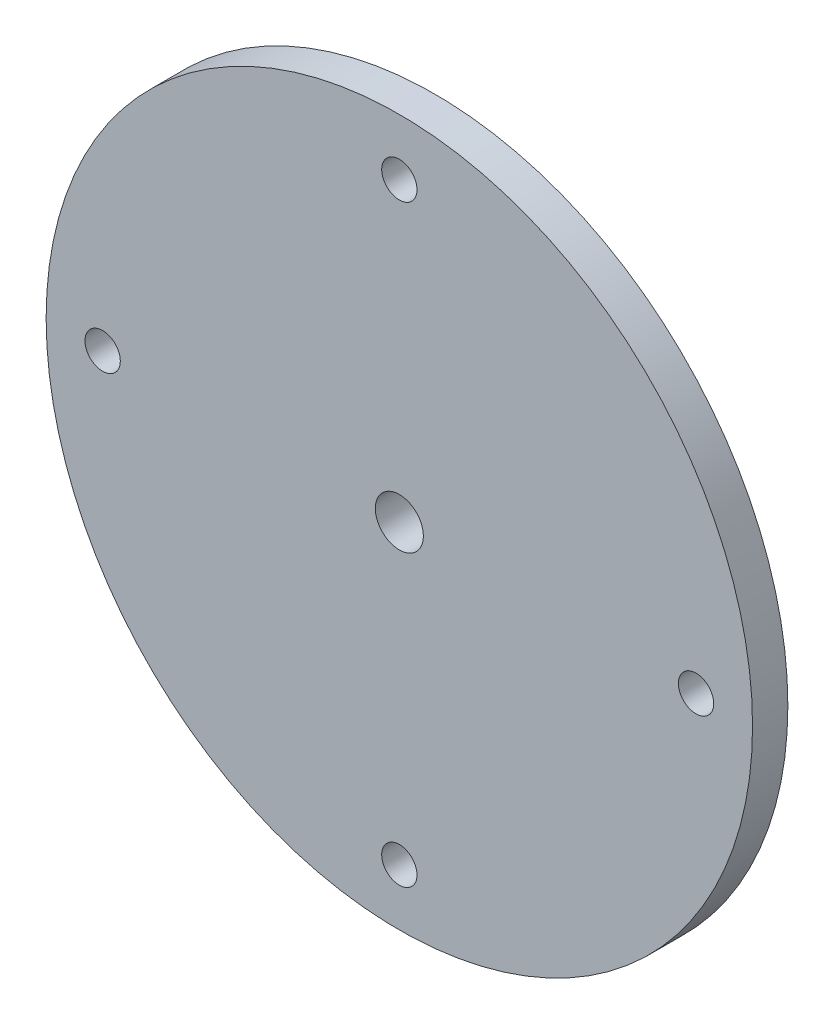
SolidWorks part; units mm, degrees
material "6061 Alloy"
ref_plane "Front Plane" through (0, 0, 0) normal (0, 0, 1) x (1, 0, 0)
ref_plane "Top Plane" through (0, 0, 0) normal (0, 1, 0) x (1, 0, 0)
ref_plane "Right Plane" through (0, 0, 0) normal (1, 0, 0) x (0, 0, -1)
sketch "Sketch1" plane through (0, 0, 0) normal (0, 0, 1) x (1, 0, 0)
  circle A0 centre (0, 0) radius 14
  circle A1 centre (0, 0) radius 12.5
  dimension "D1" = 28
  dimension "D2" = 25
extrude "Boss-Extrude1" add sketch "Sketch1" along normal blind 2
sketch "Sketch2" plane through (0, 0, 2) normal (0, 0, 1) x (1, 0, 0)
  line L1 (-8.8388, -8.8388) -> (8.8388, -8.8388)
  line L2 (-8.8388, -8.8388) -> (-8.8388, 8.8388)
  line L3 (-8.8388, 8.8388) -> (8.8388, 8.8388)
  line L4 (8.8388, -8.8388) -> (8.8388, 8.8388)
  line L5 (-8.8388, -8.8388) -> (8.8388, 8.8388) construction
  line L6 (-8.8388, 8.8388) -> (8.8388, -8.8388) construction
  circle A0 centre (0, 0) radius 12.5 construction
  circle A1 centre (0, 0) radius 14
  point P0 (0, 0)
  dimension "D1" = 28
extrude "Boss-Extrude2" add sketch "Sketch2" along normal blind 5
sketch "Sketch3" plane through (0, 0, 7) normal (0, 0, 1) x (1, 0, 0)
  circle A0 centre (0, 0) radius 14
  dimension "D1" = 28
extrude "Boss-Extrude3" add sketch "Sketch3" along normal blind 5
sketch "Sketch6" plane through (0, 0, 12) normal (0, 0, 1) x (1, 0, 0)
  circle A0 centre (0, 0) radius 50
  dimension "D1" = 100
extrude "Boss-Extrude4" add sketch "Sketch6" against normal blind 5
hole_wizard "M8x1.25 Tapped Hole1" positions "Sketch7" profile "Sketch8" tap size "M8x1.25" standard "ANSI Metric" end condition through all
sketch "Sketch7" plane through (0, 0, 12) normal (0, 0, 1) x (1, 0, 0)
  point P0 (0, 0)
cosmetic thread "Hole Thread1" parameters "D2"=8
sketch "Sketch8" plane through (0, 0, 12) normal (1, 0, 0) x (0, -1, 0)
  line L0 (0, 0) -> (0, 12)
  line L1 (0, 12) -> (3.4, 12)
  line L2 (3.4, 12) -> (3.4, 0)
  line L5 (3.4, 0) -> (0, 0)
  line L11 (0, -6.35) -> (0, 107.95) construction
  dimension "Thru Tap Drill Dia." = 6.8
  dimension "Thru Tap Drill Depth" = 12
hole_wizard "M6x1.0 Tapped Hole1" positions "Sketch9" profile "Sketch10" tap size "M6x1.0" standard "ANSI Metric" end condition through all
sketch "Sketch9" plane through (0, 0, 12) normal (0, 0, 1) x (1, 0, 0)
  line L0 (0, -6.6) -> (0, 6.6) construction
  line L1 (6.6, 0) -> (-6.6, 0) construction
  circle A0 centre (0, 0) radius 42
  point P0 (0, 42)
  point P4 (42, 0)
  point P8 (0, -42)
  point P10 (-42, 0)
  dimension "D1" = 84
sketch "Sketch10" plane through (0, 42, 12) normal (1, 0, 0) x (0, -1, 0)
  line L0 (0, 0) -> (0, 12)
  line L1 (0, 12) -> (2.5, 12)
  line L2 (2.5, 12) -> (2.5, 0)
  line L5 (2.5, 0) -> (0, 0)
  line L11 (0, -6.35) -> (0, 107.95) construction
  dimension "Thru Tap Drill Dia." = 5
  dimension "Thru Tap Drill Depth" = 12
cosmetic thread "Hole Thread2" parameters "D2"=6
cosmetic thread "Hole Thread3" parameters "D2"=6
cosmetic thread "Hole Thread4" parameters "D2"=6
cosmetic thread "Hole Thread5" parameters "D2"=6
fillet "Fillet1" radius 6 1 edges at (14, 0, 7)
